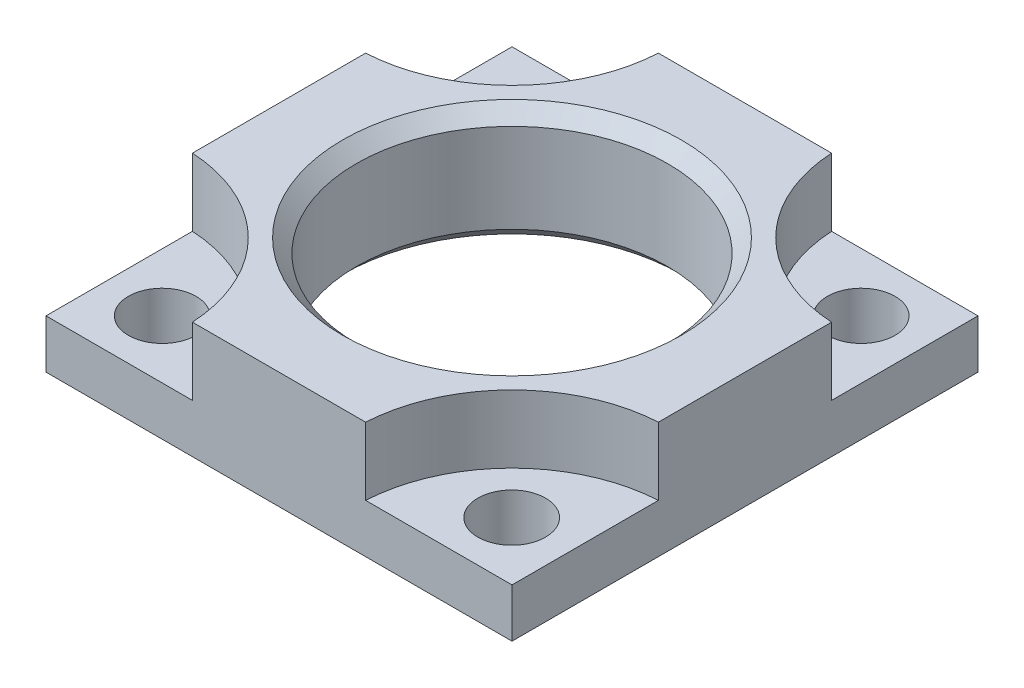
SolidWorks part; units mm, degrees
material "Alloy Steel"
ref_plane "Front Plane" through (0, 0, 0) normal (0, 0, 1) x (1, 0, 0)
ref_plane "Top Plane" through (0, 0, 0) normal (0, 1, 0) x (1, 0, 0)
ref_plane "Right Plane" through (0, 0, 0) normal (1, 0, 0) x (0, 0, -1)
sketch "Sketch1" plane through (0, 0, 0) normal (0, 1, 0) x (1, 0, 0)
  line L0 (19.05, 19.05) -> (-19.05, -19.05) construction
  line L1 (-19.05, 19.05) -> (19.05, 19.05)
  line L2 (-19.05, 19.05) -> (-19.05, -19.05)
  line L3 (-19.05, -19.05) -> (19.05, -19.05)
  line L4 (19.05, 19.05) -> (19.05, -19.05)
  line L5 (-19.05, 19.05) -> (19.05, -19.05) construction
  circle A0 centre (0, 0) radius 12.7254
  dimension "D3" = 25.4508
  dimension "D1" = 38.1
  dimension "D2" = 38.1
extrude "Extrude1" add sketch "Sketch1" along normal blind 9.525
sketch "Sketch2" plane through (0, 9.525, 0) normal (0, 1, 0) x (1, 0, 0)
  line L0 (-19.05, -19.05) -> (19.05, -19.05) construction
  line L1 (19.05, -19.05) -> (19.05, 19.05) construction
  line L2 (7.0811, -19.05) -> (19.05, -19.05)
  line L3 (19.05, -19.05) -> (19.05, -7.0811)
  line L4 (0, 0) -> (-25.3528, 0) construction
  line L5 (0, 0) -> (0, 27.5861) construction
  line L6 (19.05, 19.05) -> (19.05, 7.0811)
  line L7 (7.0811, 19.05) -> (19.05, 19.05)
  line L8 (-7.0811, 19.05) -> (-19.05, 19.05)
  line L9 (-19.05, 19.05) -> (-19.05, 7.0811)
  line L10 (-19.05, -19.05) -> (-19.05, -7.0811)
  line L11 (-7.0811, -19.05) -> (-19.05, -19.05)
  arc A0 (19.05, -7.0811) -> (7.0811, -19.05) centre (19.7612, -19.7612) ccw
  arc A1 (19.05, 7.0811) -> (7.0811, 19.05) centre (19.7612, 19.7612) cw
  arc A2 (-19.05, 7.0811) -> (-7.0811, 19.05) centre (-19.7612, 19.7612) ccw
  arc A3 (-19.05, -7.0811) -> (-7.0811, -19.05) centre (-19.7612, -19.7612) cw
  dimension "D1" = 12.7
  dimension "D2" = 19.7612
  dimension "D3" = 19.7612
extrude "Cut-Extrude1" cut sketch "Sketch2" against normal blind 5.5372
hole_wizard "Hole1" positions "Sketch4" profile "Sketch3" legacy end condition up to next
sketch "Sketch4" plane through (0, 3.9878, 0) normal (0, 1, 0) x (-1, 0, 0)
  point P0 (14.3002, 14.3002)
  point P6 (14.3002, -14.2748)
  point P9 (-14.2748, 14.3002)
  point P11 (-14.2748, -14.2748)
  dimension "D1" = 14.3002
  dimension "D2" = 14.3002
  dimension "D3" = 28.575
  dimension "D4" = 28.575
sketch "Sketch3" plane through (-14.3002, 3.9878, 14.3002) normal (1, 0, 0) x (0, 0, 1)
  line L0 (0, 0) -> (0, 3.9878)
  line L1 (0, 3.9878) -> (2.7686, 3.9878)
  line L2 (2.7686, 3.9878) -> (2.7686, 0)
  line L3 (2.7686, 0) -> (0, 0)
  line L4 (0, 110) -> (0, -10) construction
  dimension "Diameter" = 5.5372
  dimension "Depth" = 3.9878
sketch "Sketch5" plane through (0, 0, 0) normal (1, 0, 0) x (0, 0, -1)
  line L0 (0, 0) -> (0, 13.7269) construction
  line L1 (-22.3145, 4.7625) -> (-9.8575, 4.7625) construction
  line L2 (-7.0811, 9.525) -> (-19.05, 9.525) construction
  line L3 (-19.05, 0) -> (19.05, 0) construction
  line L4 (-13.843, 9.525) -> (-12.7254, 9.525)
  line L5 (-12.7254, 9.525) -> (-12.7254, 8.4074)
  line L6 (-12.7254, 9.525) -> (-12.7254, 0) construction
  line L7 (-12.7254, 8.4074) -> (-13.843, 9.525)
  line L8 (-12.7254, 1.1176) -> (-13.843, 0)
  line L9 (-12.7254, 0) -> (-12.7254, 1.1176)
  line L10 (-13.843, 0) -> (-12.7254, 0)
  dimension "D1" = 45
  dimension "D2" = 27.686
revolve "Cut-Revolve1" cut sketch "Sketch5" angle 360 about L0
